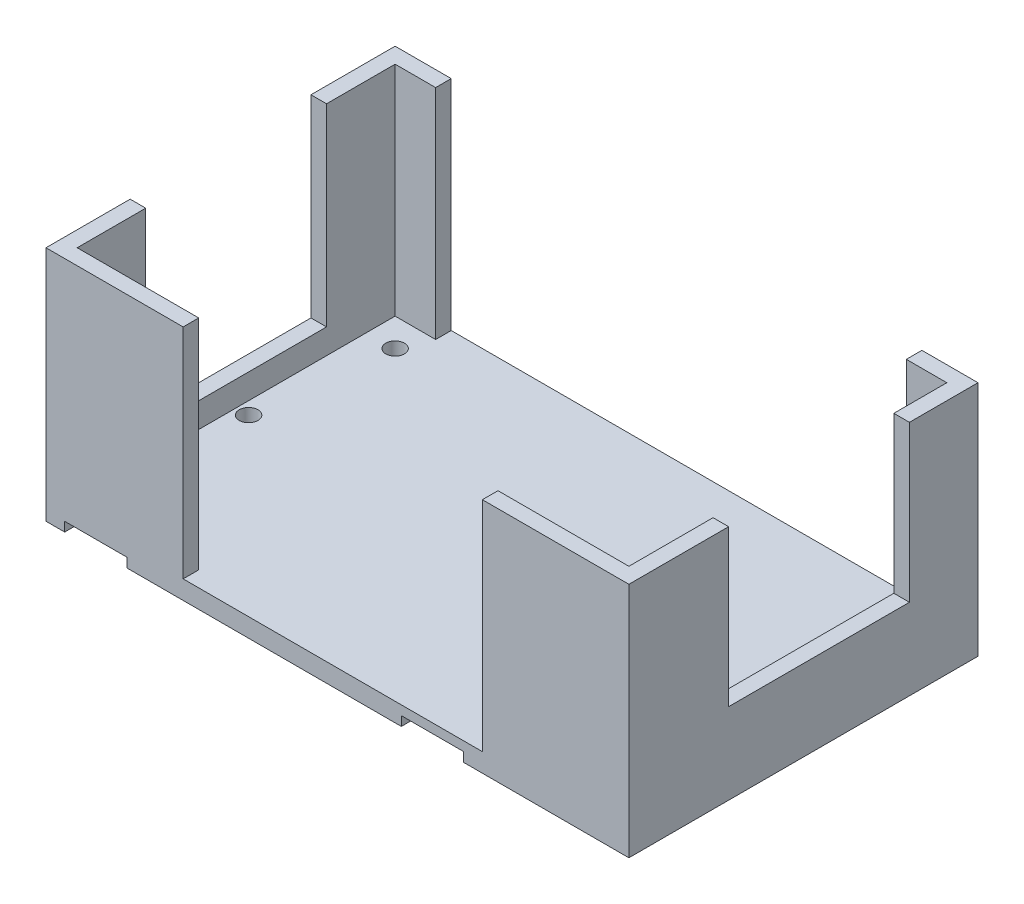
SolidWorks part; units mm, degrees
ref_plane "Front Plane" through (0, 0, 0) normal (0, 0, 1) x (1, 0, 0)
ref_plane "Top Plane" through (0, 0, 0) normal (0, 1, 0) x (1, 0, 0)
ref_plane "Right Plane" through (0, 0, 0) normal (1, 0, 0) x (0, 0, -1)
sketch "Sketch2" plane through (0, 0, 0) normal (0, 1, 0) x (1, 0, 0)
  line L1 (-76.4862, 28.6019) -> (17.0138, 28.6019)
  line L2 (-76.4862, 28.6019) -> (-76.4862, -27.3981)
  line L3 (-76.4862, -27.3981) -> (17.0138, -27.3981)
  line L4 (17.0138, 28.6019) -> (17.0138, -27.3981)
  dimension "D1" = 56
  dimension "D2" = 93.5
extrude "Boss-Extrude1" add sketch "Sketch2" along normal blind 3
sketch "Sketch3" plane through (0, 3, 0) normal (0, 1, 0) x (1, 0, 0)
  line L0 (17.0138, -27.3981) -> (17.0138, 28.6019) construction
  line L1 (17.0138, 28.6019) -> (-76.4862, 28.6019) construction
  circle A0 centre (-13.4862, 12.6019) radius 1.5
  circle A1 centre (-13.4862, -11.3981) radius 1.5
  circle A2 centre (-71.9862, 0.6019) radius 1.5
  dimension "D1" = 3
  dimension "D2" = 3
  dimension "D3" = 3
  dimension "D4" = 30.5
  dimension "D5" = 24
  dimension "D6" = 30.5
  dimension "D7" = 16
  dimension "D8" = 58.5
  dimension "D9" = 28
extrude "Cut-Extrude5" cut sketch "Sketch3" against normal through all
sketch "Sketch5" plane through (0, 0, 0) normal (0, -1, 0) x (-1, 0, 0)
  line L0 (-17.0138, 28.6019) -> (76.4862, 28.6019) construction
  circle A0 centre (26.4862, 15.8519) radius 3.025
  circle A2 centre (26.4862, -14.6481) radius 3.025
  circle A3 centre (56.9862, -14.6481) radius 3.025
  circle A4 centre (56.9862, 15.8519) radius 3.025
  circle A6 centre (13.4862, -11.3981) radius 1.5 construction
  circle A7 centre (13.4862, 12.6019) radius 1.5 construction
  dimension "D1" = 6.05
  dimension "D2" = 6.05
  dimension "D3" = 6.05
  dimension "D4" = 6.05
  dimension "D7" = 13
  dimension "D5" = 30.5
  dimension "D6" = 12.75
  dimension "D8" = 13
  dimension "D9" = 30.5
  dimension "D10" = 30.5
  dimension "D11" = 30.5
  dimension "D12" = 12.75
extrude "Cut-Extrude7" cut sketch "Sketch5" against normal blind 2.5
sketch "Sketch6" plane through (0, 3, 0) normal (0, 1, 0) x (1, 0, 0)
  line L0 (17.0138, -27.3981) -> (17.0138, 28.6019) construction
  line L1 (14.5138, 28.6019) -> (17.0138, 28.6019)
  line L2 (14.5138, 28.6019) -> (14.5138, 17.6019)
  line L3 (14.5138, 17.6019) -> (17.0138, 17.6019)
  line L4 (17.0138, 28.6019) -> (17.0138, 17.6019)
  line L5 (14.5138, -11.3981) -> (17.0138, -11.3981)
  line L6 (14.5138, -11.3981) -> (14.5138, -27.3981)
  line L7 (14.5138, -27.3981) -> (17.0138, -27.3981)
  line L8 (17.0138, -11.3981) -> (17.0138, -27.3981)
  line L9 (17.0138, 28.6019) -> (-76.4862, 28.6019) construction
  line L10 (-76.4862, -27.3981) -> (17.0138, -27.3981) construction
  line L11 (-76.4862, 28.6019) -> (-76.4862, -27.3981) construction
  line L12 (8.0138, 28.6019) -> (17.0138, 28.6019)
  line L13 (8.0138, 28.6019) -> (8.0138, 26.1019)
  line L14 (8.0138, 26.1019) -> (17.0138, 26.1019)
  line L15 (17.0138, 28.6019) -> (17.0138, 26.1019)
  line L16 (-6.4862, -24.8981) -> (14.5138, -24.8981)
  line L17 (-6.4862, -24.8981) -> (-6.4862, -27.3981)
  line L18 (-6.4862, -27.3981) -> (14.5138, -27.3981)
  line L19 (14.5138, -24.8981) -> (14.5138, -27.3981)
  line L20 (-76.4862, -24.8981) -> (-54.4862, -24.8981)
  line L21 (-76.4862, -24.8981) -> (-76.4862, -27.3981)
  line L22 (-76.4862, -27.3981) -> (-54.4862, -27.3981)
  line L23 (-54.4862, -24.8981) -> (-54.4862, -27.3981)
  line L24 (-76.4862, -13.8981) -> (-73.9862, -13.8981)
  line L25 (-76.4862, -13.8981) -> (-76.4862, -24.8981)
  line L26 (-76.4862, -24.8981) -> (-73.9862, -24.8981)
  line L27 (-73.9862, -13.8981) -> (-73.9862, -24.8981)
  line L28 (-76.4862, 26.1019) -> (-73.9862, 26.1019)
  line L29 (-76.4862, 26.1019) -> (-76.4862, 15.1019)
  line L30 (-76.4862, 15.1019) -> (-73.9862, 15.1019)
  line L31 (-73.9862, 26.1019) -> (-73.9862, 15.1019)
  line L32 (-76.4862, 28.6019) -> (-67.4862, 28.6019)
  line L33 (-76.4862, 28.6019) -> (-76.4862, 26.1019)
  line L34 (-76.4862, 26.1019) -> (-67.4862, 26.1019)
  line L35 (-67.4862, 28.6019) -> (-67.4862, 26.1019)
  dimension "D1" = 11
  dimension "D2" = 2.5
  dimension "D3" = 2.5
  dimension "D4" = 16
  dimension "D5" = 0
  dimension "D6" = 0
  dimension "D7" = 0
  dimension "D8" = 0
  dimension "D9" = 2.5
  dimension "D10" = 9
  dimension "D11" = 2.5
  dimension "D12" = 9
  dimension "D13" = 0
  dimension "D14" = 0
  dimension "D15" = 0
  dimension "D16" = 0
  dimension "D17" = 2.5
  dimension "D18" = 2.5
  dimension "D19" = 11
  dimension "D20" = 11
  dimension "D21" = 2.5
  dimension "D22" = 2.5
  dimension "D23" = 22
  dimension "D24" = 21
  dimension "D25" = 0
  dimension "D26" = 0
  dimension "D27" = 0
  dimension "D28" = 0
  dimension "D29" = 0
  dimension "D30" = 0
  dimension "D31" = 0
  dimension "D32" = 0
extrude "Boss-Extrude2" add sketch "Sketch6" along normal blind 35 contours L31 L30 L29 L28 | L32 L35 L34 L33 | L12 L15 L14 L13 | L2 L3 L4 L1 | L6 L7 L8 L5 | L16 L19 L18 L17 | L20 L23 L22 L21 | L25 L26 L27 L24
sketch "Sketch8" plane through (0, 3, 0) normal (0, 1, 0) x (1, 0, 0)
  line L1 (-73.9862, 26.1019) -> (-67.4862, 26.1019) construction
  line L2 (-73.9862, -13.8981) -> (-73.9862, -24.8981) construction
  line L3 (-73.9862, 26.1019) -> (-73.9862, 15.1019) construction
  line L4 (-73.9862, 26.1019) -> (-67.4862, 26.1019) construction
  line L5 (14.5138, 26.1019) -> (14.5138, 17.6019) construction
  line L7 (14.5138, -11.3981) -> (14.5138, -24.8981) construction
  circle A0 centre (-69.4862, -20.3981) radius 1.5
  circle A1 centre (-69.4862, 21.6019) radius 1.5
  circle A2 centre (9.5138, -20.3981) radius 1.5
  circle A3 centre (9.5138, 21.6019) radius 1.5
  dimension "D1" = 3
  dimension "D2" = 3
  dimension "D3" = 3
  dimension "D4" = 3
  dimension "D5" = 42
  dimension "D6" = 4.5
  dimension "D7" = 4.5
  dimension "D8" = 4.5
  dimension "D9" = 4.5
  dimension "D10" = 5
  dimension "D11" = 42
  dimension "D12" = 5
extrude "Cut-Extrude8" cut sketch "Sketch8" against normal through all
sketch "Sketch9" plane through (0, 0, 0) normal (0, -1, 0) x (-1, 0, 0)
  line L0 (76.4862, 28.6019) -> (76.4862, -27.3981) construction
  line L1 (73.4862, 26.6019) -> (63.4862, 26.6019)
  line L2 (73.4862, 26.6019) -> (73.4862, 28.6019)
  line L3 (73.4862, 28.6019) -> (63.4862, 28.6019)
  line L4 (63.4862, 26.6019) -> (63.4862, 28.6019)
  line L5 (73.4862, -25.3981) -> (63.4862, -25.3981)
  line L6 (73.4862, -25.3981) -> (73.4862, -27.3981)
  line L7 (73.4862, -27.3981) -> (63.4862, -27.3981)
  line L8 (63.4862, -25.3981) -> (63.4862, -27.3981)
  line L9 (19.4862, 28.6019) -> (9.4862, 28.6019)
  line L10 (19.4862, 28.6019) -> (19.4862, 26.6019)
  line L11 (19.4862, 26.6019) -> (9.4862, 26.6019)
  line L12 (9.4862, 28.6019) -> (9.4862, 26.6019)
  line L13 (19.4862, -27.3981) -> (9.4862, -27.3981)
  line L14 (19.4862, -27.3981) -> (19.4862, -25.3981)
  line L15 (19.4862, -25.3981) -> (9.4862, -25.3981)
  line L16 (9.4862, -27.3981) -> (9.4862, -25.3981)
  line L17 (-17.0138, 28.6019) -> (76.4862, 28.6019) construction
  line L18 (76.4862, -27.3981) -> (-17.0138, -27.3981) construction
  point P20 (73.4862, -26.3981)
  dimension "D1" = 2
  dimension "D2" = 2
  dimension "D3" = 2
  dimension "D4" = 2
  dimension "D5" = 3
  dimension "D6" = 0
  dimension "D7" = 10
  dimension "D8" = 10
  dimension "D9" = 10
  dimension "D10" = 0
  dimension "D11" = 44
  dimension "D12" = 3
  dimension "D13" = 0
  dimension "D14" = 10
  dimension "D15" = 0
  dimension "D16" = 44
extrude "Cut-Extrude9" cut sketch "Sketch9" against normal blind 1.5
sketch "Sketch11" plane through (0, 3, 0) normal (0, 1, 0) x (1, 0, 0)
  line L7 (17.0138, -11.3981) -> (17.0138, 17.6019) construction
  line L8 (17.0138, -11.3981) -> (14.5138, -11.3981)
  line L9 (17.0138, -11.3981) -> (17.0138, 17.6019)
  line L10 (17.0138, 17.6019) -> (14.5138, 17.6019)
  line L11 (14.5138, -11.3981) -> (14.5138, 17.6019)
  line L12 (14.5138, 17.6019) -> (17.0138, 17.6019) construction
  line L13 (14.5138, -11.3981) -> (17.0138, -11.3981) construction
  dimension "D5" = 2.5
  dimension "D6" = 0
  dimension "D7" = 0
  dimension "D8" = 0
extrude "Boss-Extrude4" add sketch "Sketch11" along normal blind 10
sketch "Sketch12" plane through (0, 3, 0) normal (0, 1, 0) x (1, 0, 0)
  line L0 (-76.4862, 15.1019) -> (-76.4862, -13.8981) construction
  line L1 (-76.4862, 15.1019) -> (-73.9862, 15.1019)
  line L2 (-76.4862, 15.1019) -> (-76.4862, -13.8981)
  line L3 (-76.4862, -13.8981) -> (-73.9862, -13.8981)
  line L4 (-73.9862, 15.1019) -> (-73.9862, -13.8981)
  line L5 (-76.4862, 15.1019) -> (-73.9862, 15.1019) construction
  line L6 (-76.4862, -13.8981) -> (-73.9862, -13.8981) construction
  dimension "D1" = 0
  dimension "D2" = 2.5
  dimension "D3" = 0
  dimension "D4" = 0
extrude "Boss-Extrude5" add sketch "Sketch12" along normal blind 4 contours L2 L1 L4 L3
